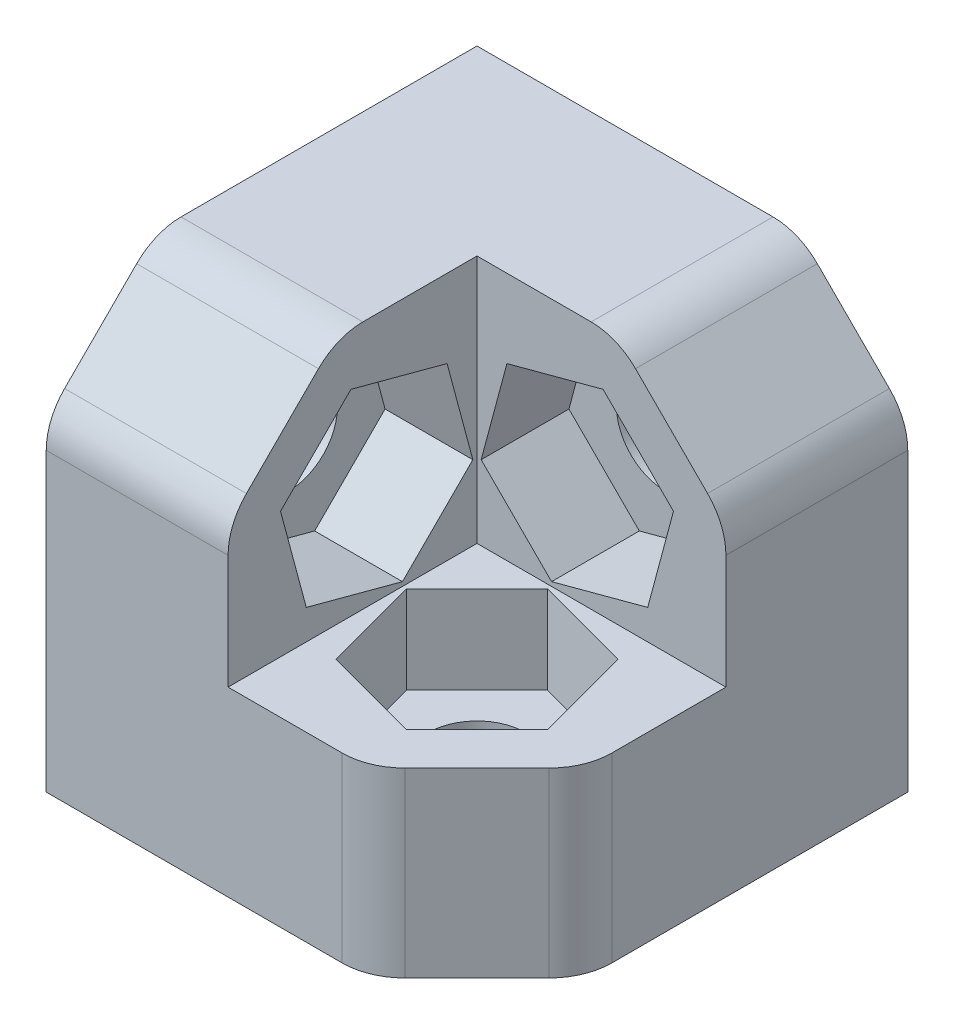
SolidWorks part; units mm, degrees
ref_plane "Ön Düzlem" through (0, 0, 0) normal (0, 0, 1) x (1, 0, 0)
ref_plane "Üst Düzlem" through (0, 0, 0) normal (0, 1, 0) x (1, 0, 0)
ref_plane "Sağ Düzlem" through (0, 0, 0) normal (1, 0, 0) x (0, 0, -1)
sketch "Çizim1" plane through (0, 0, 0) normal (0, 0, 1) x (1, 0, 0)
  line L0 (0, 0) -> (0, -15)
  line L1 (0, -15) -> (15, -15)
  line L2 (15, -15) -> (15, 0)
  line L3 (15, 0) -> (0, 0)
  circle A0 centre (9, -6) radius 1.55
  dimension "D1" = 3.1
  dimension "D2" = 9
  dimension "D3" = 15
  dimension "D4" = 9
  dimension "D5" = 15
extrude "Yükseklik-Ekstrüzyon1" add sketch "Çizim1" along normal blind 3
sketch "Çizim2" plane through (0, 0, 3) normal (0, 0, 1) x (1, 0, 0)
  line L0 (0, 0) -> (0, -15)
  line L1 (0, -15) -> (15, -15)
  line L2 (15, -15) -> (15, -12)
  line L3 (15, -15) -> (15, 0) construction
  line L4 (15, -12) -> (3, -12)
  line L5 (3, -12) -> (3, 0)
  line L6 (15, 0) -> (0, 0) construction
  line L7 (3, 0) -> (0, 0)
  dimension "D1" = 3
  dimension "D2" = 3
extrude "Yükseklik-Ekstrüzyon2" add sketch "Çizim2" along normal blind 12
sketch "Çizim3" plane through (0, -12, 0) normal (0, 1, 0) x (1, 0, 0)
  line L1 (15, 0) -> (0, 0) construction
  line L2 (0, -15) -> (0, 0) construction
  circle A0 centre (9, -9) radius 1.55
  dimension "D1" = 9
  dimension "D2" = 9
  dimension "D3" = 3.1
extrude "Kes-Ekstrüzyon1" cut sketch "Çizim3" against normal through all
sketch "Çizim4" plane through (3, 0, 0) normal (1, 0, 0) x (0, 0, -1)
  line L0 (0, -15) -> (0, 0) construction
  line L1 (-15, -15) -> (0, -15) construction
  circle A0 centre (-9, -6) radius 1.55
  dimension "D1" = 3.1
  dimension "D2" = 9
  dimension "D3" = 9
extrude "Kes-Ekstrüzyon2" cut sketch "Çizim4" against normal through all
sketch "Çizim5" plane through (0, 0, 3) normal (0, 0, 1) x (1, 0, 0)
  line L1 (12.0672, -5.1781) -> (9.8219, -2.9328)
  line L2 (9.8219, -2.9328) -> (6.7546, -3.7546)
  line L3 (6.7546, -3.7546) -> (5.9328, -6.8219)
  line L4 (5.9328, -6.8219) -> (8.1781, -9.0672)
  line L5 (8.1781, -9.0672) -> (11.2454, -8.2454)
  line L6 (11.2454, -8.2454) -> (12.0672, -5.1781)
  line L10 (13.7403, -4.7299) -> (10.2701, -1.2597)
  line L12 (15, -12) -> (15, 0) construction
  line L13 (10.2701, -1.2597) -> (5.5299, -2.5299) construction
  line L14 (4.2597, -7.2701) -> (7.7299, -10.7403) construction
  line L15 (5.5299, -2.5299) -> (4.2597, -7.2701) construction
  line L16 (7.7299, -10.7403) -> (12.4701, -9.4701) construction
  line L17 (12.4701, -9.4701) -> (13.7403, -4.7299) construction
  line L18 (13.7403, -4.7299) -> (13.7403, -12)
  line L19 (15, -12) -> (3, -12) construction
  line L20 (13.7403, -12) -> (3, -12)
  line L21 (3, -12) -> (3, -1.2597)
  line L22 (3, -12) -> (3, 0) construction
  line L23 (3, -1.2597) -> (10.2701, -1.2597)
  circle A0 centre (9, -6) radius 2.75 construction
  dimension "D1" = 5.5
  dimension "D3" = 45
  dimension "D2" = 1.5
extrude "Yükseklik-Ekstrüzyon3" add sketch "Çizim5" along normal blind 2.8
sketch "Çizim6" plane through (0, -12, 0) normal (0, 1, 0) x (1, 0, 0)
  line L1 (12.0672, -9.8219) -> (11.2454, -6.7546)
  line L2 (11.2454, -6.7546) -> (8.1781, -5.9328)
  line L3 (8.1781, -5.9328) -> (5.9328, -8.1781)
  line L4 (5.9328, -8.1781) -> (6.7546, -11.2454)
  line L5 (6.7546, -11.2454) -> (9.8219, -12.0672)
  line L6 (9.8219, -12.0672) -> (12.0672, -9.8219)
  line L9 (10.2701, -13.7403) -> (13.7403, -10.2701)
  line L12 (15, -15) -> (15, -3) construction
  line L13 (10.2701, -13.7403) -> (5.5299, -13.7403)
  line L16 (5.5299, -12.4701) -> (10.2701, -13.7403) construction
  line L19 (5.5299, -13.7403) -> (3, -13.7403)
  line L20 (13.7403, -10.2701) -> (12.4701, -5.5299) construction
  line L21 (3, -15) -> (3, -3) construction
  line L22 (3, -13.7403) -> (3, -3)
  line L23 (3, -3) -> (13.7403, -3)
  line L24 (13.7403, -10.2701) -> (13.7403, -3)
  line L26 (4.2597, -7.7299) -> (5.5299, -12.4701) construction
  line L27 (7.7299, -4.2597) -> (4.2597, -7.7299) construction
  line L28 (12.4701, -5.5299) -> (7.7299, -4.2597) construction
  circle A0 centre (9, -9) radius 2.75 construction
  point P18 (0, 0)
  point P20 (0, 0)
  point P21 (0, 0)
  dimension "D1" = 5.5
  dimension "D3" = 45
  dimension "D4" = 10.7403
  dimension "D2" = 1.5
extrude "Yükseklik-Ekstrüzyon4" add sketch "Çizim6" along normal blind 2.8
sketch "Çizim7" plane through (3, 0, 0) normal (1, 0, 0) x (0, 0, -1)
  line L0 (-10.2701, -1.2597) -> (-13.7403, -4.7299)
  line L1 (-11.2454, -8.2454) -> (-8.1781, -9.0672)
  line L2 (-8.1781, -9.0672) -> (-5.9328, -6.8219)
  line L3 (-5.9328, -6.8219) -> (-6.7546, -3.7546)
  line L4 (-6.7546, -3.7546) -> (-9.8219, -2.9328)
  line L5 (-9.8219, -2.9328) -> (-12.0672, -5.1781)
  line L6 (-12.0672, -5.1781) -> (-11.2454, -8.2454)
  line L12 (-15, -12) -> (-15, 0) construction
  line L13 (-13.7403, -4.7299) -> (-12.4701, -9.4701) construction
  line L14 (-12.4701, -9.4701) -> (-7.7299, -10.7403) construction
  line L15 (-7.7299, -10.7403) -> (-4.2597, -7.2701) construction
  line L16 (-4.2597, -7.2701) -> (-5.5299, -2.5299) construction
  line L17 (-5.5299, -2.5299) -> (-10.2701, -1.2597) construction
  line L18 (-10.2701, -1.2597) -> (-3, -1.2597)
  line L19 (-3, -1.2597) -> (-3, -12)
  line L20 (-3, -12) -> (-13.7403, -12)
  line L21 (-13.7403, -4.7299) -> (-13.7403, -12)
  circle A0 centre (-9, -6) radius 2.75 construction
  dimension "D1" = 5.5
  dimension "D3" = 45
  dimension "D2" = 1.5
extrude "Yükseklik-Ekstrüzyon5" add sketch "Çizim7" along normal blind 2.8
sketch "Çizim9" plane through (0, 0, 3) normal (0, 0, 1) x (1, 0, 0)
  line L0 (9.0104, 0) -> (15, -5.9896)
  line L3 (9.0104, 0) -> (15, 0)
  line L4 (15, 0) -> (15, -5.9896)
  line L5 (13.7403, -4.7299) -> (10.2701, -1.2597) construction
extrude "Kes-Ekstrüzyon3" cut sketch "Çizim9" against normal blind 3
sketch "Çizim10" plane through (0, -12, 0) normal (0, 1, 0) x (1, 0, 0)
  line L0 (15, -9.0104) -> (9.0104, -15)
  line L3 (15, -9.0104) -> (15, -15)
  line L4 (15, -15) -> (9.0104, -15)
  line L5 (10.2701, -13.7403) -> (13.7403, -10.2701) construction
extrude "Kes-Ekstrüzyon4" cut sketch "Çizim10" against normal blind 3
sketch "Çizim11" plane through (3, 0, 0) normal (1, 0, 0) x (0, 0, -1)
  line L0 (-9.0104, 0) -> (-15, -5.9896)
  line L3 (-15, -5.9896) -> (-15, 0)
  line L4 (-15, 0) -> (-9.0104, 0)
  line L5 (-10.2701, -1.2597) -> (-13.7403, -4.7299) construction
extrude "Kes-Ekstrüzyon5" cut sketch "Çizim11" against normal blind 3 contours L0 L3 L4
sketch "Çizim13" plane through (15, 0, 0) normal (1, 0, 0) x (0, 0, -1)
  line L0 (-13.7403, -2.9481) -> (-13.7403, -15.7979)
  line L1 (-13.7403, -15.7979) -> (-15.7895, -15.7979)
  line L2 (-15.7895, -15.7979) -> (-15.7895, -2.9481)
  line L3 (-15.7895, -2.9481) -> (-13.7403, -2.9481)
  line L5 (-9.0104, -15) -> (-15, -15) construction
  line L6 (-13.7403, -9.2) -> (-13.7403, -12) construction
  dimension "D1" = 12.8497
  dimension "D2" = 0.7979
  dimension "D3" = 2.0493
extrude "Kes-Ekstrüzyon6" cut sketch "Çizim13" against normal blind 16
sketch "Çizim14" plane through (0, 0, 13.7403) normal (0, 0, 1) x (1, 0, 0)
  line L1 (15, -15) -> (13.7403, -15)
  line L2 (15, -15) -> (15, -4.7299)
  line L3 (15, -4.7299) -> (13.7403, -4.7299)
  line L4 (13.7403, -15) -> (13.7403, -4.7299)
extrude "Kes-Ekstrüzyon7" cut sketch "Çizim14" against normal blind 16 contours L2 L3 L4 L1
sketch "Çizim15" plane through (13.7403, 0, 0) normal (1, 0, 0) x (0, 0, -1)
  line L1 (0, 0) -> (-10.2701, 0)
  line L2 (0, 0) -> (0, -1.2597)
  line L3 (0, -1.2597) -> (-10.2701, -1.2597)
  line L4 (-10.2701, 0) -> (-10.2701, -1.2597)
extrude "Kes-Ekstrüzyon8" cut sketch "Çizim15" against normal blind 16
fillet "Radyus1" radius 2 6 edges at (2.9, -4.7299, 13.7403) (2.9, -1.2597, 10.2701) (10.2701, -1.2597, 2.9) (13.7403, -4.7299, 2.9) (13.7403, -12.1, 10.2701) (10.2701, -12.1, 13.7403)
